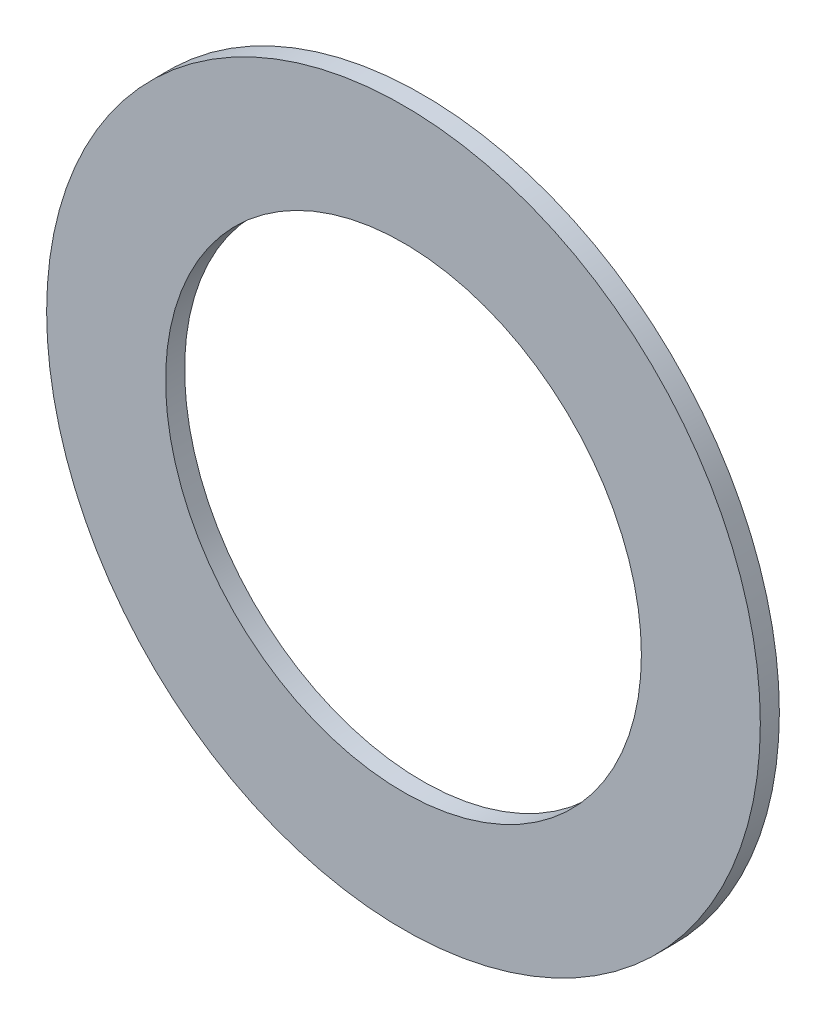
SolidWorks part; units mm, degrees
ref_plane "Front Plane" through (0, 0, 0) normal (0, 0, 1) x (1, 0, 0)
ref_plane "Top Plane" through (0, 0, 0) normal (0, 1, 0) x (1, 0, 0)
ref_plane "Right Plane" through (0, 0, 0) normal (1, 0, 0) x (0, 0, -1)
sketch "Sketch1" plane through (0, 0, 0) normal (0, 0, 1) x (1, 0, 0)
  circle A0 centre (0, 0) radius 4.7625
  circle A1 centre (0, 0) radius 3.175
  dimension "D1" = 9.525
  dimension "D2" = 6.35
extrude "Extrude1" add sketch "Sketch1" along normal blind 0.254
